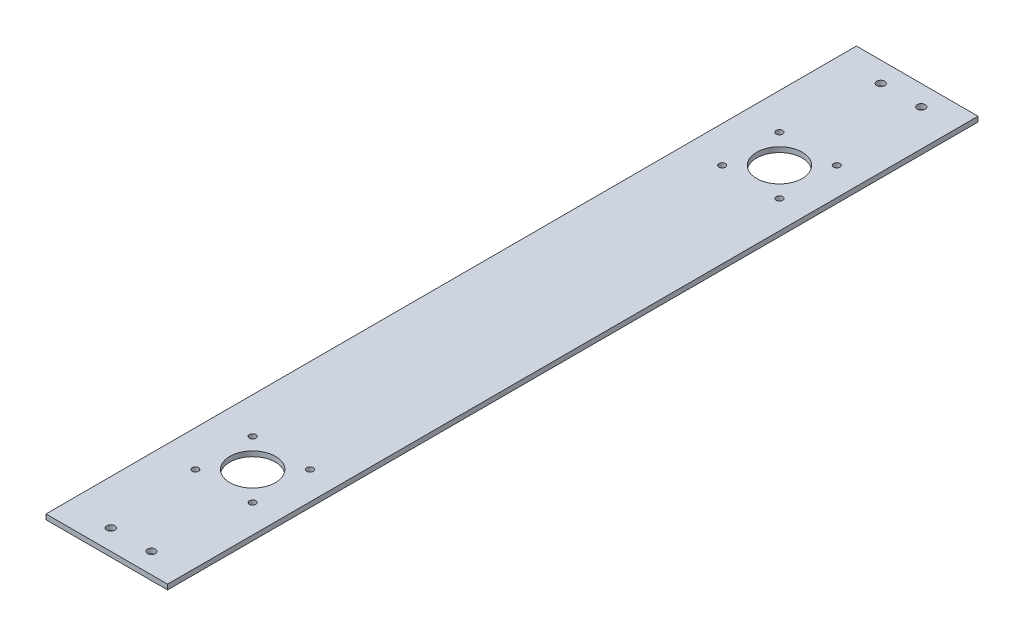
SolidWorks part; units mm, degrees
material "Lexan"
ref_plane "Front Plane" through (0, 0, 0) normal (0, 0, 1) x (1, 0, 0)
ref_plane "Top Plane" through (0, 0, 0) normal (0, 1, 0) x (1, 0, 0)
ref_plane "Right Plane" through (0, 0, 0) normal (1, 0, 0) x (0, 0, -1)
sketch "Sketch1" plane through (0, 0, 0) normal (0, 1, 0) x (1, 0, 0)
  line L1 (0, 0) -> (406.4, 0)
  line L2 (0, 0) -> (0, 508)
  line L3 (0, 508) -> (406.4, 508)
  line L4 (406.4, 0) -> (406.4, 508)
  dimension "D1" = 406.4
  dimension "D2" = 508
extrude "Boss-Extrude1" add sketch "Sketch1" along normal blind 3.175
sketch "Sketch2" plane through (0, 3.175, 0) normal (0, 1, 0) x (1, 0, 0)
  line L0 (107.95, 419.1) -> (107.95, 508) construction
  line L1 (50.8, 419.1) -> (165.1, 419.1) construction
  line L2 (406.4, 0) -> (406.4, 508) construction
  line L3 (50.8, 88.9) -> (165.1, 88.9) construction
  line L5 (406.4, 508) -> (0, 508) construction
  line L6 (107.95, 88.9) -> (107.95, 0) construction
  line L7 (0, 0) -> (406.4, 0) construction
  circle A0 centre (50.8, 419.1) radius 14.2875
  circle A1 centre (165.1, 419.1) radius 14.2875
  circle A2 centre (50.8, 88.9) radius 14.2875
  circle A3 centre (165.1, 88.9) radius 14.2875
  dimension "D1" = 28.575
  dimension "D2" = 28.575
  dimension "D3" = 28.575
  dimension "D4" = 28.575
  dimension "D5" = 114.3
  dimension "D6" = 114.3
  dimension "D7" = 330.2
  dimension "D9" = 241.3
extrude "Cut-Extrude1" cut sketch "Sketch2" against normal blind 3.175
sketch "Sketch3" plane through (0, 3.175, 0) normal (0, 1, 0) x (1, 0, 0)
  line L0 (0, 12.7) -> (124.5108, 12.7) construction
  line L1 (0, 508) -> (0, 0) construction
  line L2 (406.4, 0) -> (406.4, 508) construction
  line L3 (0, 0) -> (406.4, 0) construction
  line L4 (101.6, 0) -> (101.6, 12.7) construction
  line L5 (0, 254) -> (406.4, 254) construction
  line L6 (101.6, 508) -> (101.6, 495.3) construction
  line L7 (0, 495.3) -> (124.5108, 495.3) construction
  line L8 (129.4892, 495.3) -> (406.4, 495.3) construction
  line L9 (129.4892, 12.7) -> (406.4, 12.7) construction
  circle A0 centre (38.1, 12.7) radius 2.4892
  circle A1 centre (63.5, 12.7) radius 2.4892
  circle A3 centre (152.4, 12.7) radius 2.4892
  circle A4 centre (177.8, 12.7) radius 2.4892
  circle A5 centre (203.2, 12.7) radius 2.4892
  circle A6 centre (228.6, 12.7) radius 2.4892
  circle A7 centre (254, 12.7) radius 2.4892
  circle A8 centre (279.4, 12.7) radius 2.4892
  circle A9 centre (304.8, 12.7) radius 2.4892
  circle A10 centre (330.2, 12.7) radius 2.4892
  circle A11 centre (355.6, 12.7) radius 2.4892
  circle A12 centre (381, 12.7) radius 2.4892
  circle A13 centre (381, 495.3) radius 2.4892
  circle A14 centre (355.6, 495.3) radius 2.4892
  circle A15 centre (330.2, 495.3) radius 2.4892
  circle A16 centre (304.8, 495.3) radius 2.4892
  circle A17 centre (279.4, 495.3) radius 2.4892
  circle A18 centre (254, 495.3) radius 2.4892
  circle A19 centre (228.6, 495.3) radius 2.4892
  circle A20 centre (203.2, 495.3) radius 2.4892
  circle A21 centre (177.8, 495.3) radius 2.4892
  circle A22 centre (152.4, 495.3) radius 2.4892
  circle A24 centre (63.5, 495.3) radius 2.4892
  circle A25 centre (38.1, 495.3) radius 2.4892
  circle A27 centre (101.6, 12.7) radius 2.4892
  dimension "D1" = 4.9784
  dimension "D2" = 38.1
  dimension "D4" = 25.4
  dimension "D3" = 12.7
  dimension "D5" = 38.1
extrude "Cut-Extrude2" cut sketch "Sketch3" against normal through all both and the other way through all
sketch "Sketch4" plane through (0, 3.175, 0) normal (0, 1, 0) x (1, 0, 0)
  line L0 (25.4, 419.1) -> (38.1, 441.097) construction
  line L1 (38.1, 441.097) -> (63.5, 441.097) construction
  line L2 (63.5, 441.097) -> (76.2, 419.1) construction
  line L3 (76.2, 419.1) -> (63.5, 397.103) construction
  line L4 (63.5, 397.103) -> (38.1, 397.103) construction
  line L5 (38.1, 397.103) -> (25.4, 419.1) construction
  line L6 (0, 254) -> (406.4, 254) construction
  line L7 (183.0605, 401.1395) -> (147.1395, 401.1395) construction
  line L8 (183.0605, 401.1395) -> (183.0605, 437.0605) construction
  line L9 (183.0605, 437.0605) -> (147.1395, 437.0605) construction
  line L10 (147.1395, 401.1395) -> (147.1395, 437.0605) construction
  line L11 (183.0605, 401.1395) -> (147.1395, 437.0605) construction
  line L12 (183.0605, 437.0605) -> (147.1395, 401.1395) construction
  line L13 (0, 508) -> (0, 0) construction
  line L14 (406.4, 0) -> (406.4, 508) construction
  line L15 (183.0605, 70.9395) -> (147.1395, 106.8605) construction
  line L16 (183.0605, 106.8605) -> (147.1395, 70.9395) construction
  line L17 (147.1395, 106.8605) -> (147.1395, 70.9395) construction
  line L18 (183.0605, 70.9395) -> (147.1395, 70.9395) construction
  line L19 (183.0605, 106.8605) -> (183.0605, 70.9395) construction
  line L20 (183.0605, 106.8605) -> (147.1395, 106.8605) construction
  line L21 (38.1, 110.897) -> (25.4, 88.9) construction
  line L22 (63.5, 110.897) -> (38.1, 110.897) construction
  line L23 (76.2, 88.9) -> (63.5, 110.897) construction
  line L24 (63.5, 66.903) -> (76.2, 88.9) construction
  line L25 (38.1, 66.903) -> (63.5, 66.903) construction
  line L26 (25.4, 88.9) -> (38.1, 66.903) construction
  circle A0 centre (50.8, 419.1) radius 25.4 construction
  circle A1 centre (76.2, 419.1) radius 2.0193
  circle A2 centre (25.4, 419.1) radius 2.0193
  circle A3 centre (38.1, 441.097) radius 2.0193
  circle A4 centre (63.5, 441.097) radius 2.0193
  circle A5 centre (63.5, 397.103) radius 2.0193
  circle A6 centre (38.1, 397.103) radius 2.0193
  circle A7 centre (147.1395, 437.0605) radius 2.0193
  circle A8 centre (183.0605, 437.0605) radius 2.0193
  circle A9 centre (183.0605, 401.1395) radius 2.0193
  circle A10 centre (147.1395, 401.1395) radius 2.0193
  circle A11 centre (50.8, 88.9) radius 25.4 construction
  circle A12 centre (147.1395, 106.8605) radius 2.0193
  circle A13 centre (183.0605, 106.8605) radius 2.0193
  circle A14 centre (183.0605, 70.9395) radius 2.0193
  circle A15 centre (147.1395, 70.9395) radius 2.0193
  circle A16 centre (38.1, 110.897) radius 2.0193
  circle A17 centre (63.5, 110.897) radius 2.0193
  circle A18 centre (63.5, 66.903) radius 2.0193
  circle A19 centre (38.1, 66.903) radius 2.0193
  circle A20 centre (25.4, 88.9) radius 2.0193
  circle A21 centre (76.2, 88.9) radius 2.0193
  point P15 (165.1, 419.1)
  point P53 (165.1, 88.9)
  dimension "D1" = 50.8
  dimension "D2" = 4.0386
  dimension "D5" = 4.0386
  dimension "D3" = 35.921
  dimension "D4" = 35.921
extrude "Cut-Extrude3" cut sketch "Sketch4" against normal through all both and the other way through all
sketch "Sketch5" plane through (0, 3.175, 0) normal (0, 1, 0) x (1, 0, 0)
  line L0 (0, 0) -> (406.4, 0) construction
  line L1 (0, 508) -> (124.46, 508)
  line L2 (0, 508) -> (0, 0)
  line L3 (0, 0) -> (124.46, 0)
  line L4 (124.46, 508) -> (124.46, 0)
  line L6 (406.4, 508) -> (200.66, 508)
  line L7 (406.4, 508) -> (406.4, 0)
  line L8 (406.4, 0) -> (200.66, 0)
  line L9 (200.66, 508) -> (200.66, 0)
  dimension "D1" = 205.74
  dimension "D2" = 76.2
extrude "Cut-Extrude4" cut sketch "Sketch5" against normal up to next
